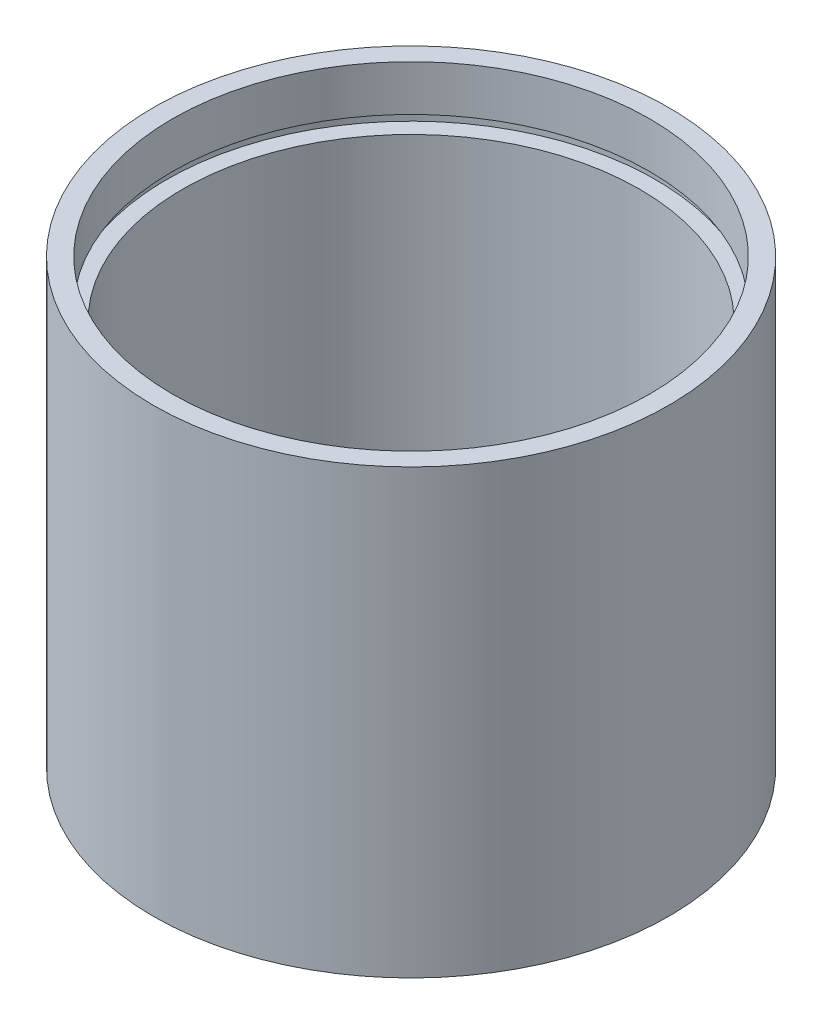
SolidWorks part; units mm, degrees
ref_plane "前视基准面" through (0, 0, 0) normal (0, 0, 1) x (1, 0, 0)
ref_plane "上视基准面" through (0, 0, 0) normal (0, 1, 0) x (1, 0, 0)
ref_plane "右视基准面" through (0, 0, 0) normal (1, 0, 0) x (0, 0, -1)
sketch "草图1" plane through (0, 0, 0) normal (0, 0, 1) x (1, 0, 0)
  line L0 (0, 161.3762) -> (0, 0) construction
  line L1 (141.7365, 0) -> (-131.7984, 0) construction
  line L2 (25.4, 0) -> (25.4, 43.6)
  line L3 (23.5, 0) -> (23.5, 4.5)
  line L4 (24.1, 4.5) -> (24.1, 5.5)
  line L5 (22.5, 5.5) -> (22.5, 38.1)
  line L6 (22.5, 5.5) -> (24.1, 5.5)
  line L7 (24.1, 38.1) -> (24.1, 39.1)
  line L8 (22.5, 38.1) -> (24.1, 38.1)
  line L9 (23.5, 39.1) -> (23.5, 43.6)
  line L10 (24.1, 39.1) -> (23.5, 39.1)
  line L11 (23.5, 43.6) -> (25.4, 43.6)
  line L12 (23.5, 0) -> (25.4, 0)
  line L13 (23.5, 4.5) -> (24.1, 4.5)
  dimension "D1" = 25.4
  dimension "D2" = 23.5
  dimension "D3" = 4.5
  dimension "D4" = 24.1
  dimension "D5" = 22.5
  dimension "D6" = 24.1
  dimension "D7" = 1
  dimension "D8" = 5.5
  dimension "D9" = 38.1
  dimension "D10" = 1
revolve "旋转1" add sketch "草图1" angle 360 about L0
cosmetic thread "装饰螺纹线1" parameters "D2"=48
cosmetic thread "装饰螺纹线2" parameters "D2"=46
cosmetic thread "装饰螺纹线3" parameters "D2"=48
